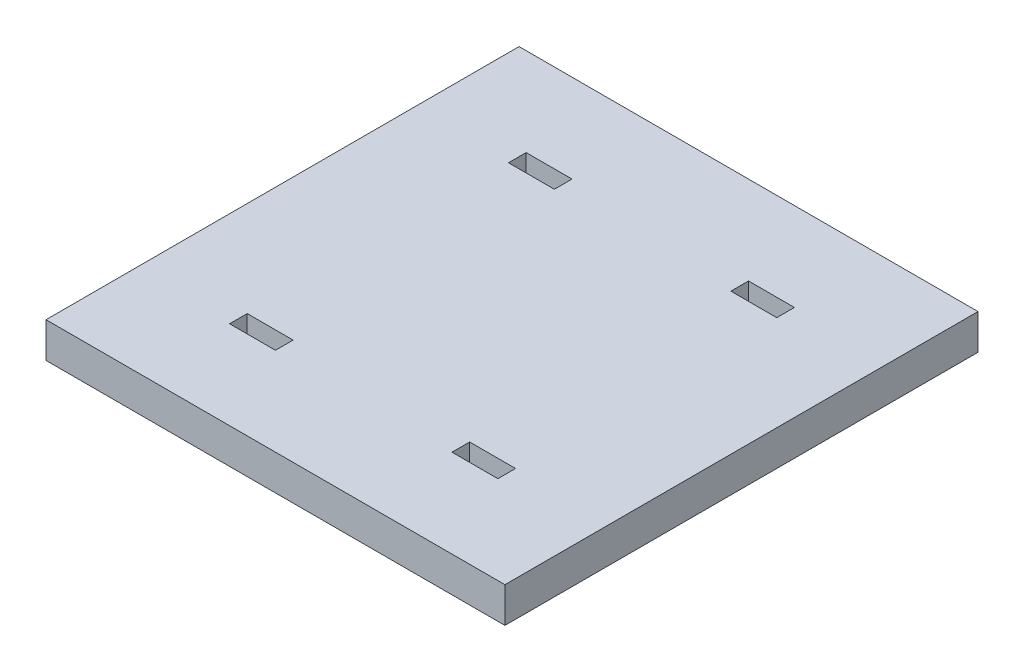
SolidWorks part; units mm, degrees
ref_plane "Alzado" through (0, 0, 0) normal (0, 0, 1) x (1, 0, 0)
ref_plane "Planta" through (0, 0, 0) normal (0, 1, 0) x (1, 0, 0)
ref_plane "Vista lateral" through (0, 0, 0) normal (1, 0, 0) x (0, 0, -1)
sketch "Croquis1" plane through (0, 0, 0) normal (0, 1, 0) x (1, 0, 0)
  line L0 (65, 134) -> (65, 0) construction
  line L2 (0, 0) -> (130, 0)
  line L3 (0, 0) -> (0, 134)
  line L4 (0, 134) -> (130, 134)
  line L5 (130, 0) -> (130, 134)
  line L6 (0, 67) -> (130, 67) construction
  line L7 (27, 106.5) -> (0, 106.5) construction
  line L8 (27, 109) -> (40, 109)
  line L9 (27, 109) -> (27, 104)
  line L10 (27, 104) -> (40, 104)
  line L12 (40, 109) -> (40, 104)
  line L13 (33.5, 109) -> (33.5, 134) construction
  line L14 (27, 30) -> (40, 30)
  line L15 (40, 25) -> (40, 30)
  line L20 (27, 25) -> (40, 25)
  line L33 (27, 25) -> (27, 30)
  line L34 (103, 25) -> (103, 30)
  line L35 (103, 25) -> (90, 25)
  line L36 (90, 25) -> (90, 30)
  line L37 (103, 30) -> (90, 30)
  line L38 (103, 104) -> (90, 104)
  line L39 (90, 109) -> (90, 104)
  line L40 (103, 109) -> (90, 109)
  line L41 (103, 109) -> (103, 104)
  dimension "D2" = 134
  dimension "D3" = 13
  dimension "D13" = 130
extrude "Saliente-Extruir1" add sketch "Croquis1" along normal blind 10
